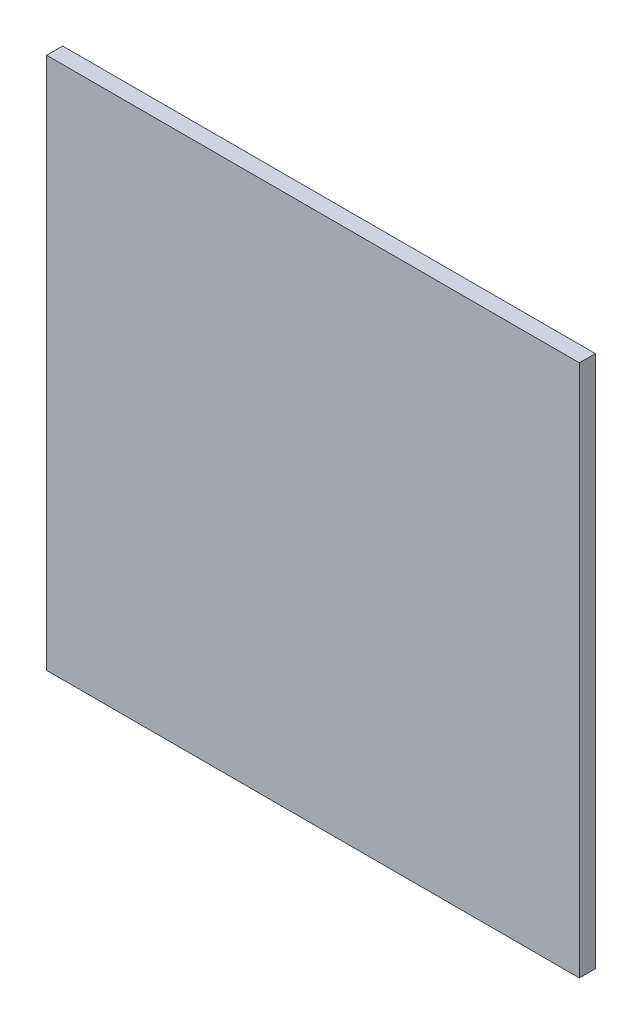
SolidWorks part; units mm, degrees
ref_plane "前视基准面" through (0, 0, 0) normal (0, 0, 1) x (1, 0, 0)
ref_plane "上视基准面" through (0, 0, 0) normal (0, 1, 0) x (1, 0, 0)
ref_plane "右视基准面" through (0, 0, 0) normal (1, 0, 0) x (0, 0, -1)
sketch "草图1" plane through (0, 0, 0) normal (0, 0, 1) x (1, 0, 0)
  line L1 (0, 0) -> (100, 0)
  line L2 (0, 0) -> (0, 100)
  line L3 (0, 100) -> (100, 100)
  line L4 (100, 0) -> (100, 100)
extrude "凸台-拉伸1" add sketch "草图1" along normal blind 3
